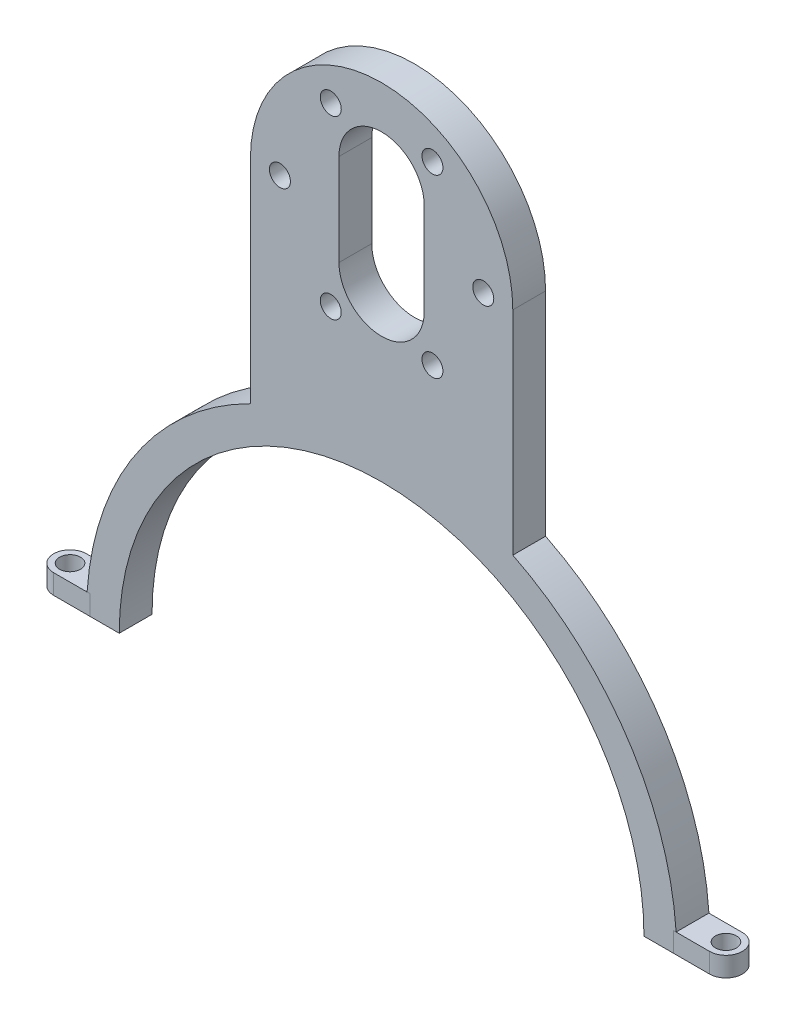
SolidWorks part; units mm, degrees
ref_plane "前视基准面" through (0, 0, 0) normal (0, 0, 1) x (1, 0, 0)
ref_plane "上视基准面" through (0, 0, 0) normal (0, 1, 0) x (1, 0, 0)
ref_plane "右视基准面" through (0, 0, 0) normal (1, 0, 0) x (0, 0, -1)
other "Configuration Table"
sketch "草图1" plane through (0, 0, 0) normal (0, 0, 1) x (1, 0, 0)
  line L0 (0, 0) -> (0, 72.7) construction
  line L1 (-20, 72.7) -> (-20, 40.3113)
  line L2 (20, 72.7) -> (20, 40.3113)
  circle A0 centre (0, 0) radius 40 construction
  circle A1 centre (0, 0) radius 40
  circle A2 centre (0, 0) radius 72.7 construction
  circle A3 centre (0, 72.7) radius 30 construction
  arc A4 (20, 72.7) -> (-20, 72.7) centre (0, 72.7) ccw
  arc A5 (-20, 40.3113) -> (20, 40.3113) centre (0, 0) ccw
  dimension "D1" = 80
  dimension "D2" = 80
  dimension "D3" = 145.4
  dimension "D4" = 40
  dimension "D5" = 90
  dimension "D6" = 60
extrude "凸台-拉伸1" add sketch "草图1" along normal blind 5
sketch "草图2" plane through (0, 0, 5) normal (0, 0, 1) x (1, 0, 0)
  line L0 (0, 79.7) -> (0, 65.7) construction
  line L1 (6.5, 79.7) -> (6.5, 65.7)
  line L2 (-6.5, 79.7) -> (-6.5, 65.7)
  line L3 (-10.911, 91.5984) -> (24989.089, -43209.6718) construction
  circle A0 centre (0, 72.7) radius 15.5 construction
  arc A1 (6.5, 79.7) -> (-6.5, 79.7) centre (0, 79.7) ccw
  arc A2 (-6.5, 65.7) -> (6.5, 65.7) centre (0, 65.7) ccw
  circle A3 centre (-7.75, 86.1234) radius 1.6
  circle A4 centre (7.75, 86.1234) radius 1.6
  circle A5 centre (15.5, 72.7) radius 1.6
  circle A6 centre (7.75, 59.2766) radius 1.6
  circle A7 centre (-7.75, 59.2766) radius 1.6
  circle A8 centre (-15.5, 72.7) radius 1.6
  point P6 (0, 72.7)
  point P11 (0, 72.7)
  point P27 (0, 72.7)
  dimension "D1" = 31
  dimension "D5" = 3.2
  dimension "D2" = 14
  dimension "D3" = 13
  dimension "D4" = 30
  dimension "D6" = 6
extrude "切除-拉伸1" cut sketch "草图2" against normal mid plane 10
sketch "草图3" plane through (0, 0, 0) normal (0, 0, -1) x (-1, 0, 0)
  circle A0 centre (-7.75, 86.1234) radius 2.6
  circle A1 centre (7.75, 86.1234) radius 2.6
  circle A2 centre (15.5, 72.7) radius 2.6
  circle A3 centre (7.75, 59.2766) radius 2.6
  circle A4 centre (-7.75, 59.2766) radius 2.6
  circle A5 centre (-15.5, 72.7) radius 2.6
  point P3 (0, 72.7)
  point P16 (0, 72.7)
  dimension "D1" = 5.2
  dimension "D2" = 6
extrude "切除-拉伸2" cut sketch "草图3" against normal blind 2
sketch "草图4" plane through (0, 0, 5) normal (0, 0, 1) x (1, 0, 0)
  line L1 (-45, 0) -> (54.2623, 0)
  line L2 (-45, 0) -> (-45, -51.8289)
  line L3 (-45, -51.8289) -> (54.2623, -51.8289)
  line L4 (54.2623, 0) -> (54.2623, -51.8289)
  arc A0 (-20, 40.3113) -> (20, 40.3113) centre (0, 0) ccw construction
extrude "切除-拉伸3" cut sketch "草图4" against normal through all both and the other way through all
sketch "草图5" plane through (0, 0, 0) normal (0, -1, 0) x (1, 0, 0)
  line L0 (0, -1000) -> (0, 49000) construction
  line L1 (-44.4725, 5) -> (-50, 5)
  line L2 (-44.4725, 5) -> (-44.4725, 0)
  line L3 (-44.4725, 0) -> (-50, 0)
  line L5 (-40, 0) -> (40, 0) construction
  line L6 (44.4725, 0) -> (50, 0)
  line L7 (44.4725, 5) -> (44.4725, 0)
  line L8 (44.4725, 5) -> (50, 5)
  line L9 (-45, 0) -> (-45, 5) construction
  arc A0 (-50, 5) -> (-50, 0) centre (-50, 2.5) ccw
  circle A1 centre (-50, 2.5) radius 1.6
  circle A2 centre (50, 2.5) radius 1.6
  arc A3 (50, 5) -> (50, 0) centre (50, 2.5) cw
  point P12 (0, 0)
  point P18 (0, 0)
  dimension "D2" = 3.2
  dimension "D1" = 5
  dimension "D3" = 5
extrude "凸台-拉伸2" add sketch "草图5" against normal blind 3 separate body
